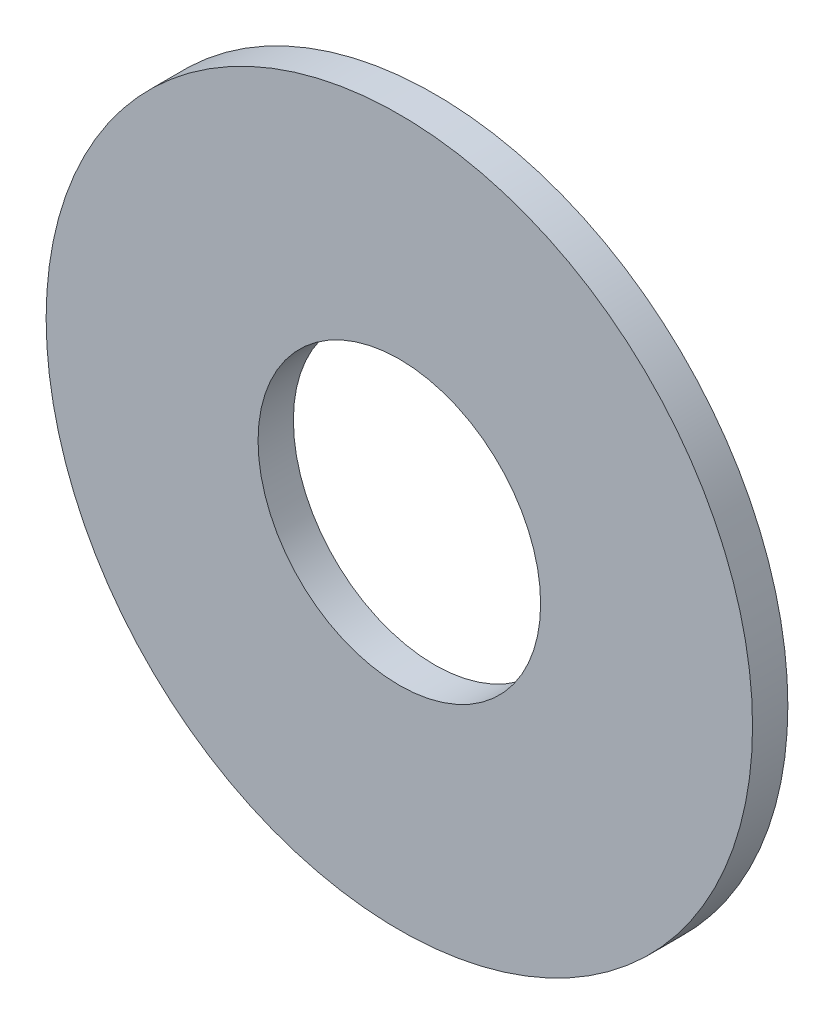
SolidWorks part; units mm, degrees
ref_plane "Plano frontal" through (0, 0, 0) normal (0, 0, 1) x (1, 0, 0)
ref_plane "Plano superior" through (0, 0, 0) normal (0, 1, 0) x (1, 0, 0)
ref_plane "Plano direito" through (0, 0, 0) normal (1, 0, 0) x (0, 0, -1)
sketch "Esboço1" plane through (0, 0, 0) normal (0, 0, 1) x (1, 0, 0)
  circle A0 centre (0, 0) radius 10
  circle A1 centre (0, 0) radius 4
extrude "Ressalto-extrusão1" add sketch "Esboço1" along normal blind 1
